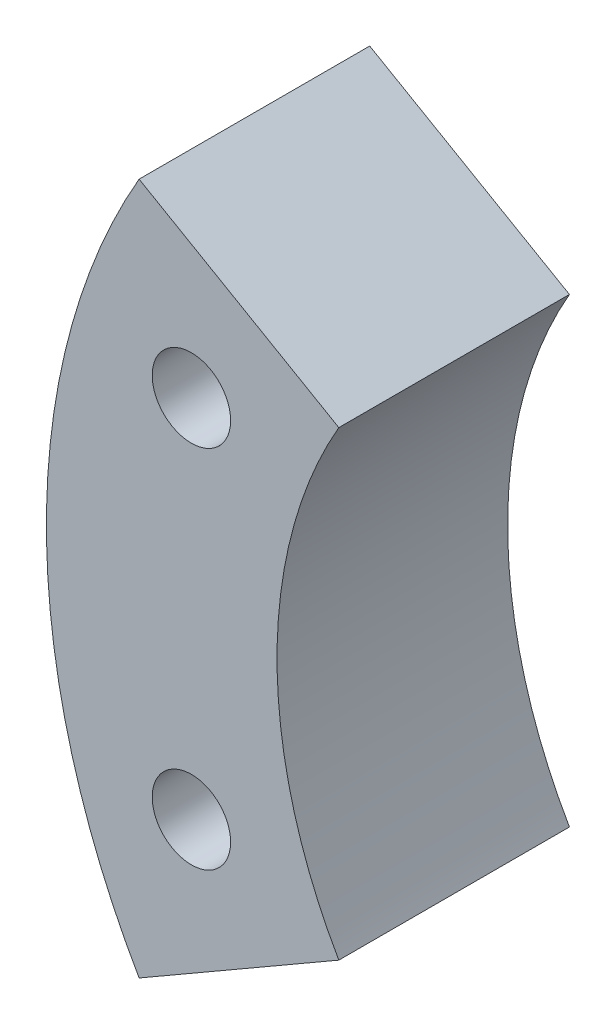
SolidWorks part; units mm, degrees
ref_plane "Front Plane" through (0, 0, 0) normal (1, 0, 0) x (0, 1, 0)
ref_plane "Top Plane" through (0, 0, 0) normal (0, 0, 1) x (0, 1, 0)
ref_plane "Right Plane" through (0, 0, 0) normal (0, 1, 0) x (-1, 0, 0)
sketch "Sketch1" plane through (0, 0, 0) normal (0, 0, 1) x (0, 1, 0)
  line L0 (0, 0) -> (9.525, 16.4978) construction
  line L1 (9.525, 16.4978) -> (-9.525, 16.4978) construction
  line L2 (-9.525, 16.4978) -> (0, 0) construction
  line L3 (-9.525, 16.4978) -> (-6.35, 10.9985)
  line L4 (9.525, 16.4978) -> (6.35, 10.9985)
  arc A0 (6.35, 10.9985) -> (-6.35, 10.9985) centre (0, 0) ccw
  arc A1 (9.525, 16.4978) -> (-9.525, 16.4978) centre (0, 0) ccw
  dimension "D1" = 25.4
  dimension "D2" = 38.1
  dimension "D3" = 19.05
extrude "Boss-Extrude1" add sketch "Sketch1" along normal blind 6.35
sketch "Sketch2" plane through (0, 0, 6.35) normal (0, 0, 1) x (1, 0, 0)
  line L0 (-10.9985, 6.35) -> (-16.4978, 9.525) construction
  line L1 (-16.4978, -9.525) -> (-10.9985, -6.35) construction
  line L2 (-15.0579, 5.0275) -> (0, 0) construction
  line L3 (0, 0) -> (-15.0579, -5.0275) construction
  circle A1 centre (-15.0579, 5.0275) radius 1.0795
  circle A2 centre (-15.0579, -5.0275) radius 1.0795
  point P3 (-15.0579, 5.0275)
  point P4 (-15.0579, -5.0275)
  dimension "D1" = 15.875
  dimension "D5" = 2.159
  dimension "D6" = 2.159
  dimension "D2" = 3.175
  dimension "D3" = 3.175
  dimension "D4" = 15.875
extrude "Cut-Extrude1" cut sketch "Sketch2" against normal up to next
